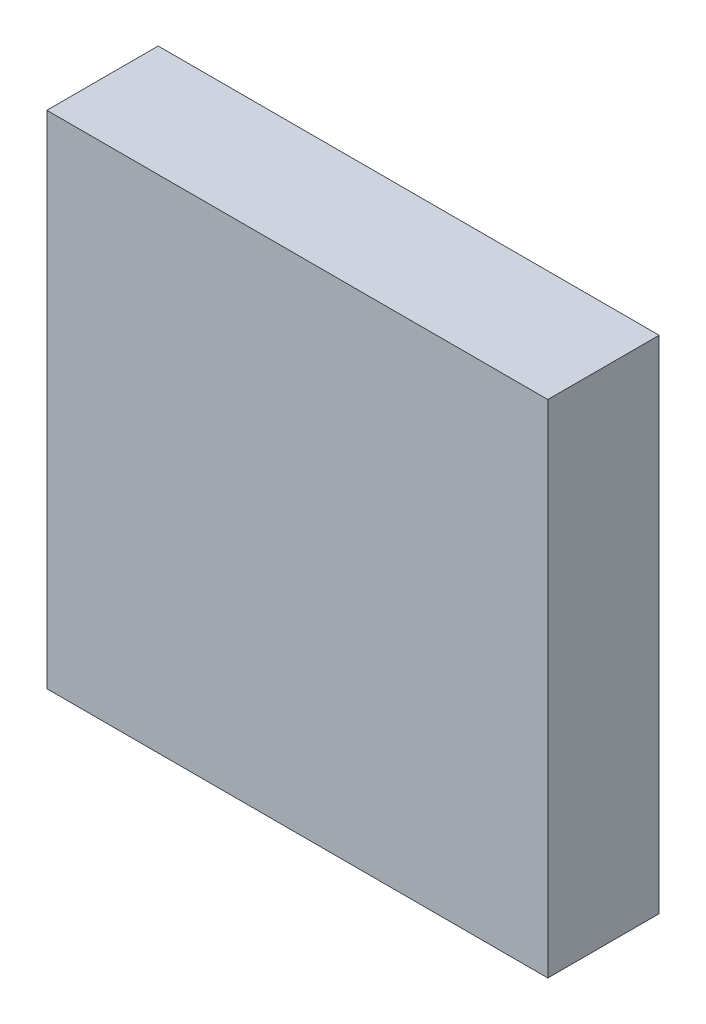
SolidWorks part; units mm, degrees
ref_plane "Alzado" through (0, 0, 0) normal (0, 0, 1) x (1, 0, 0)
ref_plane "Planta" through (0, 0, 0) normal (0, 1, 0) x (1, 0, 0)
ref_plane "Vista lateral" through (0, 0, 0) normal (1, 0, 0) x (0, 0, -1)
sketch "Croquis2" plane through (0, 0, 0) normal (0, 0, 1) x (1, 0, 0)
  line L1 (225, -225) -> (-225, -225)
  line L2 (225, -225) -> (225, 225)
  line L3 (225, 225) -> (-225, 225)
  line L4 (-225, -225) -> (-225, 225)
  line L5 (225, -225) -> (-225, 225) construction
  line L6 (225, 225) -> (-225, -225) construction
  point P0 (0, 0)
  dimension "D1" = 450
  dimension "D2" = 450
extrude "Saliente-Extruir1" add sketch "Croquis2" along normal blind 100
sketch "Croquis3" plane through (0, 0, 0) normal (0, 0, -1) x (-1, 0, 0)
  line L0 (-98.5976, 50.2985) -> (262.7358, 50.2985) construction
sketch "Croquis4" plane through (0, 0, 0) normal (0, 0, -1) x (-1, 0, 0)
  line L0 (151.0906, -171.9988) -> (180.424, -171.9988) construction
  line L1 (42.7612, -174.4988) -> (72.7612, -174.4988) construction
  line L2 (-62.3329, -169.7864) -> (-34.9996, -169.7864) construction
  line L3 (-168.9728, 118.3035) -> (-139.6395, 118.3035) construction
  line L4 (-67.0911, 129.2903) -> (-37.0911, 129.2903) construction
  line L5 (38.3593, 125.0093) -> (67.026, 125.0093) construction
sketch "Croquis5" plane through (225, 0, 0) normal (1, 0, 0) x (0, 0, -1)
  line L0 (-47.0734, 56.8168) -> (86.2599, 56.8168) construction
  line L1 (-28.9677, -129.8016) -> (199.0323, -129.8016) construction
sketch "Croquis6" plane through (0, -225, 0) normal (0, -1, 0) x (1, 0, 0)
  line L0 (-122.3025, -9.5594) -> (11.0309, -9.5594) construction
